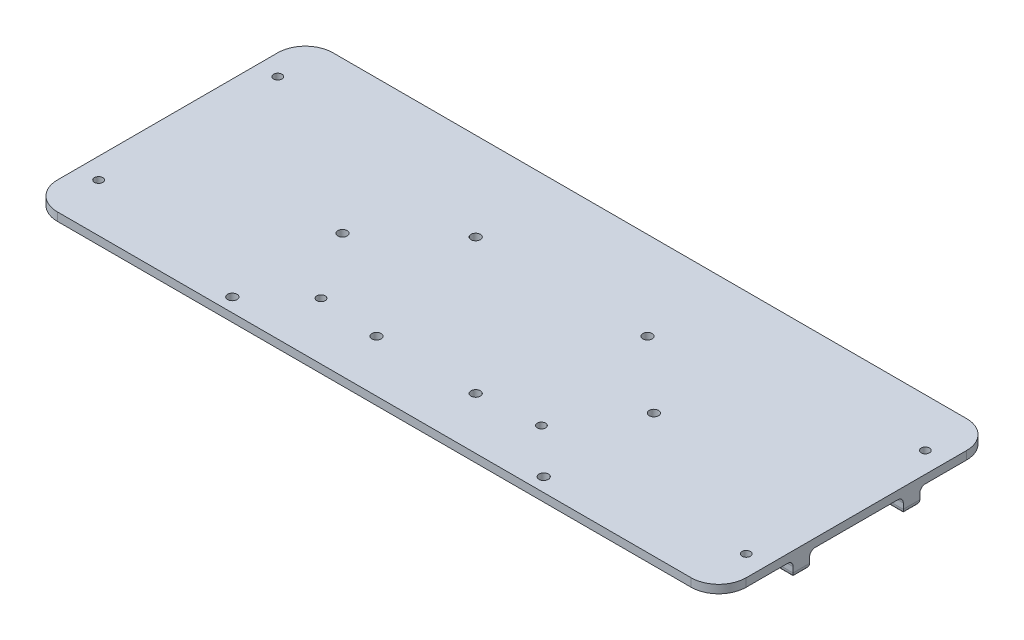
SolidWorks part; units mm, degrees
ref_plane "前视基准面" through (0, 0, 0) normal (0, 0, 1) x (1, 0, 0)
ref_plane "上视基准面" through (0, 0, 0) normal (0, 1, 0) x (1, 0, 0)
ref_plane "右视基准面" through (0, 0, 0) normal (1, 0, 0) x (0, 0, -1)
sketch "草图1" plane through (0, 0, 0) normal (0, 1, 0) x (1, 0, 0)
  line L1 (-125, 50) -> (125, 50)
  line L2 (-125, 50) -> (-125, -50)
  line L3 (-125, -50) -> (125, -50)
  line L4 (125, 50) -> (125, -50)
  line L5 (-125, 50) -> (125, -50) construction
  line L6 (-125, -50) -> (125, 50) construction
  point P0 (0, 0)
  dimension "D1" = 250
  dimension "D2" = 100
extrude "凸台-拉伸1" add sketch "草图1" along normal blind 3
fillet "圆角1" radius 10 4 edges at (-125, 1.5, -50) (125, 1.5, -50) (125, 1.5, 50) (-125, 1.5, 50)
sketch "草图2" plane through (0, 3, 0) normal (0, 1, 0) x (1, 0, 0)
  line L1 (-117.5, 32.5) -> (117.5, 32.5) construction
  line L2 (-117.5, 32.5) -> (-117.5, -32.5) construction
  line L3 (-117.5, -32.5) -> (117.5, -32.5) construction
  line L4 (117.5, 32.5) -> (117.5, -32.5) construction
  line L5 (-117.5, 32.5) -> (117.5, -32.5) construction
  line L6 (-117.5, -32.5) -> (117.5, 32.5) construction
  circle A0 centre (-117.5, 32.5) radius 1.525
  circle A1 centre (117.5, 32.5) radius 1.525
  circle A2 centre (117.5, -32.5) radius 1.525
  circle A3 centre (-117.5, -32.5) radius 1.525
  point P0 (0, 0)
  dimension "D3" = 3.05
  dimension "D4" = 3.05
  dimension "D5" = 3.05
  dimension "D6" = 3.05
  dimension "D1" = 235
  dimension "D2" = 65
extrude "切除-拉伸1" cut sketch "草图2" against normal blind 3
sketch "草图3" plane through (0, 3, 0) normal (0, 1, 0) x (1, 0, 0)
  line L0 (-40, -29.33) -> (40, -29.33) construction
  line L1 (-115, -50) -> (115, -50) construction
  circle A0 centre (-40, -29.33) radius 1.525
  circle A2 centre (40, -29.33) radius 1.525
  dimension "D1" = 3.05
  dimension "D2" = 3.05
  dimension "D3" = 80
  dimension "D4" = 20.67
extrude "切除-拉伸2" cut sketch "草图3" against normal blind 3
sketch "草图4" plane through (0, 0, 0) normal (0, -1, 0) x (1, 0, 0)
  line L0 (-125, -40) -> (-125, 40) construction
  line L1 (-125, 17) -> (125, 17)
  line L2 (-125, 17) -> (-125, 23)
  line L3 (-125, 23) -> (125, 23)
  line L4 (125, 17) -> (125, 23)
  line L5 (125, 40) -> (125, -40) construction
  line L6 (-115, 50) -> (115, 50) construction
  line L7 (-125, -23) -> (125, -23)
  line L8 (-125, -23) -> (-125, -17)
  line L9 (-125, -17) -> (125, -17)
  line L10 (125, -23) -> (125, -17)
  line L11 (115, -50) -> (-115, -50) construction
  dimension "D1" = 6
  dimension "D2" = 6
  dimension "D3" = 27
  dimension "D4" = 27
extrude "凸台-拉伸2" add sketch "草图4" along normal blind 6
fillet "圆角2" radius 2 12 edges at (0, -6, -17) (125, -6, -20) (0, -6, -23) (-125, -6, -20) (0, -6, 23) (125, -6, 20) (0, -6, 17) (-125, -6, 20) (0, 0, -23) (0, 0, -17) (0, 0, 17) (0, 0, 23)
sketch "草图5" plane through (0, 3, 0) normal (0, 1, 0) x (1, 0, 0)
  line L0 (0, 36) -> (0, -36) construction
  line L1 (-31.1769, 18) -> (0, 0) construction
  line L2 (0, 0) -> (31.1769, 18) construction
  line L3 (0, 0) -> (-18, -31.1769) construction
  line L4 (0, 0) -> (18, -31.1769) construction
  circle A0 centre (0, 0) radius 36 construction
  circle A1 centre (-31.1769, 18) radius 1.7
  circle A2 centre (31.1769, 18) radius 1.7
  circle A3 centre (-18, -31.1769) radius 1.7
  circle A4 centre (18, -31.1769) radius 1.7
  dimension "D1" = 72
  dimension "D6" = 3.4
  dimension "D2" = 60
  dimension "D3" = 60
  dimension "D4" = 30
  dimension "D5" = 30
extrude "切除-拉伸3" cut sketch "草图5" against normal up to next
sketch "草图6" plane through (0, 3, 0) normal (0, 1, 0) x (1, 0, 0)
  line L0 (-115, -50) -> (115, -50) construction
  line L1 (-56.5, -45) -> (56.5, -45) construction
  line L2 (-56.5, -45) -> (-56.5, -5) construction
  line L3 (-56.5, -5) -> (56.5, -5) construction
  line L4 (56.5, -45) -> (56.5, -5) construction
  line L5 (-56.5, -45) -> (56.5, -5) construction
  line L6 (-56.5, -5) -> (56.5, -45) construction
  circle A0 centre (-56.5, -5) radius 1.7
  circle A1 centre (56.5, -5) radius 1.7
  circle A2 centre (-56.5, -45) radius 1.7
  circle A3 centre (56.5, -45) radius 1.7
  point P0 (0, -25)
  point P7 (-56.5, -40.8524)
  point P9 (56.5, -0.7485)
  point P12 (56.5, -40.7341)
  point P16 (-55.7571, 0)
  dimension "D4" = 3.4
  dimension "D1" = 113
  dimension "D2" = 40
  dimension "D3" = 45
extrude "切除-拉伸4" cut sketch "草图6" against normal up to next
sketch "草图7" plane through (0, -6, 0) normal (0, -1, 0) x (1, 0, 0)
  line L0 (56.5, 20) -> (-56.5, 20) construction
  line L1 (0, 25) -> (0, 15) construction
  line L2 (-125, 25) -> (125, 25) construction
  line L3 (125, 15) -> (-125, 15) construction
  line L5 (-63, 15) -> (-50, 15)
  line L6 (-63, 15) -> (-63, 25)
  line L7 (-63, 25) -> (-50, 25)
  line L8 (-50, 15) -> (-50, 25)
  line L9 (-63, 15) -> (-50, 25) construction
  line L10 (-63, 25) -> (-50, 15) construction
  line L11 (50, 15) -> (63, 15)
  line L12 (50, 15) -> (50, 25)
  line L13 (50, 25) -> (63, 25)
  line L14 (63, 15) -> (63, 25)
  line L15 (50, 15) -> (63, 25) construction
  line L16 (50, 25) -> (63, 15) construction
  point P3 (0, 20)
  dimension "D1" = 113
  dimension "D2" = 13
  dimension "D3" = 13
extrude "切除-拉伸5" cut sketch "草图7" against normal blind 3
fillet "圆角3" radius 2 20 edges at (-50, -3.5, 17) (-50, -5.4142, 17.5858) (-50, -3.5, 23) (-50, -5.4142, 22.4142) (-63, -3.5, 23) (-63, -5.4142, 22.4142) (-63, -3.5, 17) (-63, -5.4142, 17.5858) (-50, -6, 20) (-63, -6, 20) (63, -3.5, 17) (63, -5.4142, 17.5858) (63, -3.5, 23) (63, -5.4142, 22.4142) (50, -3.5, 23) (50, -5.4142, 22.4142) (50, -3.5, 17) (50, -5.4142, 17.5858) (63, -6, 20) (50, -6, 20)
